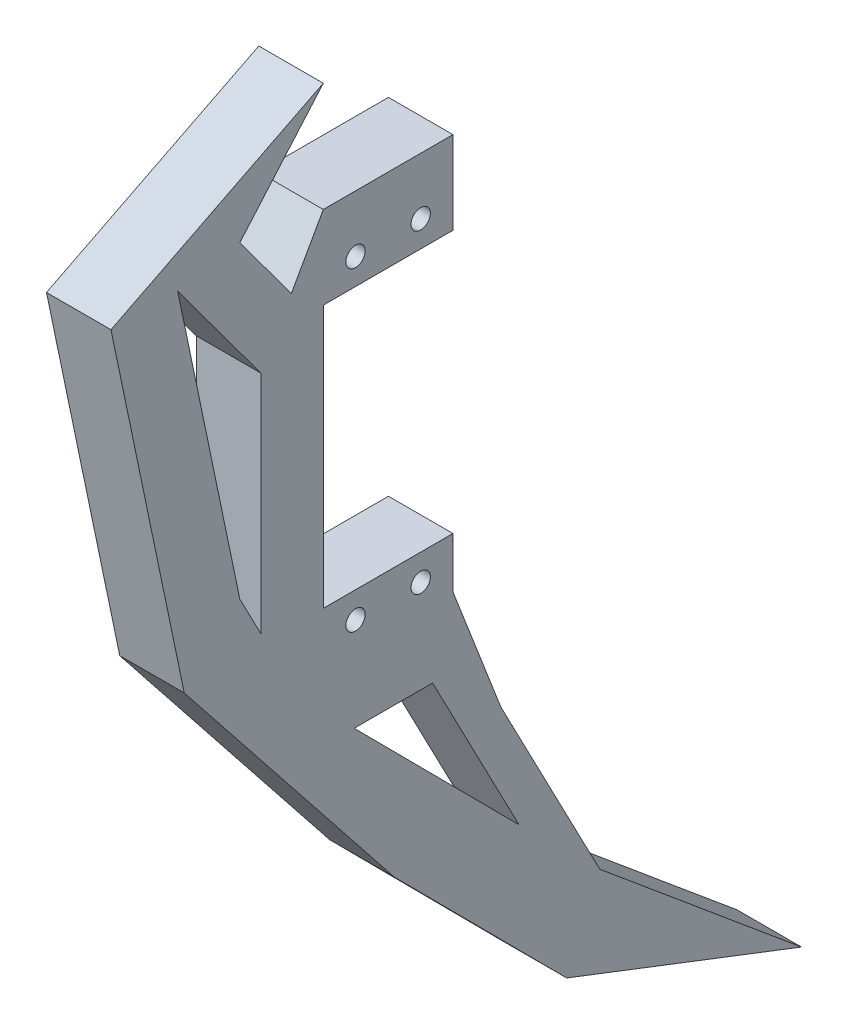
SolidWorks part; units mm, degrees
ref_plane "前视基准面" through (0, 0, 0) normal (0, 0, 1) x (1, 0, 0)
ref_plane "上视基准面" through (0, 0, 0) normal (0, 1, 0) x (1, 0, 0)
ref_plane "右视基准面" through (0, 0, 0) normal (1, 0, 0) x (0, 0, -1)
other "Configuration Table"
sketch "草图7" plane through (0, 0, 0) normal (1, 0, 0) x (0, 0, -1)
  line L0 (65.677, -92.4645) -> (74.7812, -92.4645)
  line L1 (74.7812, -105.3145) -> (74.7812, -92.4645)
  line L4 (54.6812, -92.4645) -> (65.677, -92.4645)
  line L6 (54.6812, -92.4645) -> (49.7312, -101.2645)
  line L7 (49.7312, -101.2645) -> (41.742, -90.4551)
  line L8 (41.742, -90.4551) -> (54.6812, -75.5174)
  line L9 (54.6812, -75.5174) -> (21.77, -92.1479)
  line L10 (21.77, -92.1479) -> (27.5186, -119.7042)
  line L11 (27.5186, -119.7042) -> (33.1293, -146.5991)
  line L12 (82.2179, -173.0503) -> (74.7812, -153.8645)
  line L13 (82.2179, -173.0503) -> (97.545, -202.4714)
  line L14 (128.8194, -228.5573) -> (92.4192, -214.5124)
  line L15 (92.4192, -214.5124) -> (65.677, -187.5834)
  line L16 (65.677, -187.5834) -> (33.1293, -146.5991)
  line L17 (97.545, -202.4714) -> (128.8194, -228.5573)
  line L18 (74.7812, -153.8645) -> (74.7812, -146.0145)
  line L19 (74.7812, -92.4645) -> (54.6812, -92.4645)
  line L20 (32.1112, -92.1479) -> (45.0032, -109.5907)
  line L21 (45.0032, -109.5907) -> (45.0032, -144.573)
  line L22 (45.0032, -144.573) -> (41.742, -138.313)
  line L23 (41.742, -138.313) -> (32.1112, -92.1479)
  line L24 (71.6237, -164.5137) -> (59.4733, -164.5137)
  line L25 (59.4733, -164.5137) -> (85.0314, -190.2505)
  line L26 (85.0314, -190.2505) -> (71.6237, -164.5137)
  line L27 (54.6812, -105.3145) -> (54.6812, -146.0145)
  line L29 (74.7812, -146.0145) -> (54.6812, -146.0145)
  line L30 (74.7812, -105.3145) -> (54.6812, -105.3145)
  circle A0 centre (59.6812, -101.2645) radius 1.5
  circle A1 centre (69.7812, -101.2645) radius 1.5
  circle A2 centre (59.6812, -150.0645) radius 1.5
  circle A3 centre (69.7812, -150.0645) radius 1.5
  dimension "D3" = 3
  dimension "D4" = 3
  dimension "D5" = 3
  dimension "D6" = 3
extrude "凸台-拉伸2" add sketch "草图7" along normal blind 10 contours L30 L1 L0 L4 L6 L7 L8 L9 L10 L11 L16 L15 L14 L17 L13 L12 L18 L29 L27 A3 A2 A1 A0 L26 L25 L24 L22 L23 L20 L21
